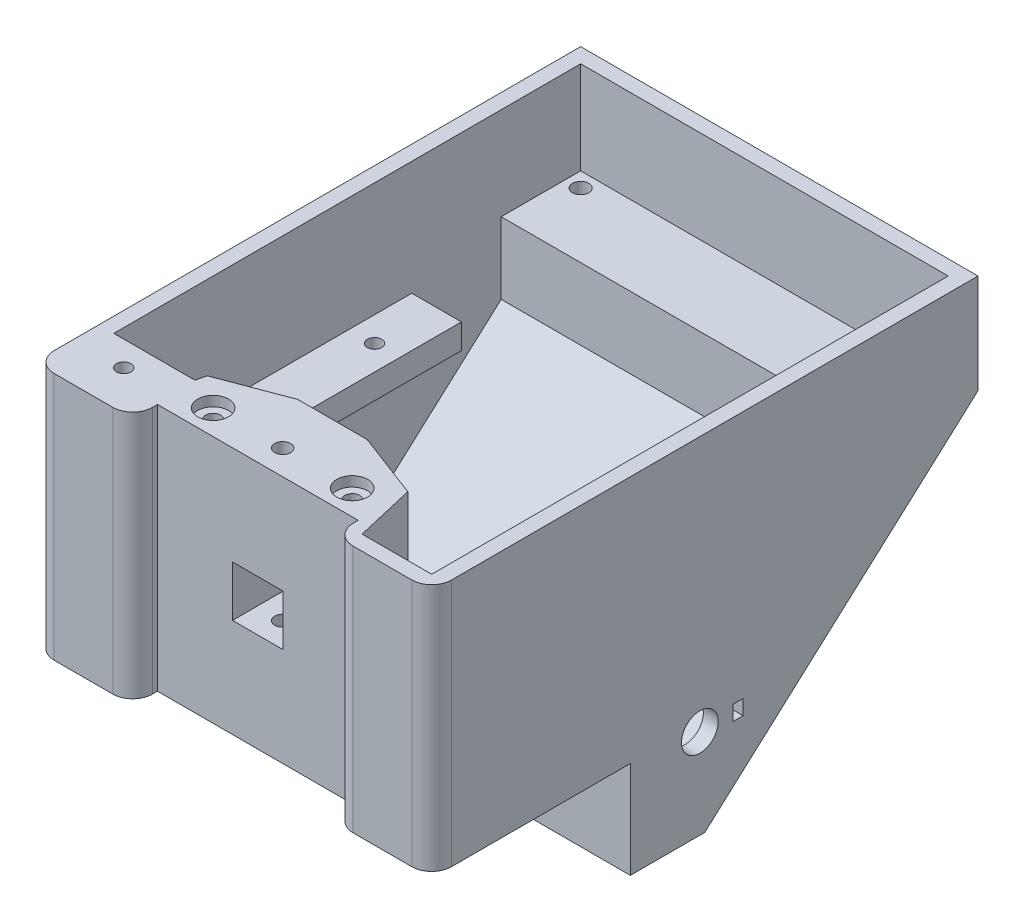
SolidWorks part; units mm, degrees
ref_plane "Спереди" through (0, 0, 0) normal (0, 0, 1) x (1, 0, 0)
ref_plane "Сверху" through (0, 0, 0) normal (0, 1, 0) x (1, 0, 0)
ref_plane "Справа" through (0, 0, 0) normal (1, 0, 0) x (0, 0, -1)
sketch "Sketch2" plane through (0, 0, 0) normal (1, 0, 0) x (0, 0, -1)
  line L0 (-27.3205, 20.9982) -> (-27.3205, -29.0018)
  line L1 (-27.3205, -29.0018) -> (12.6795, -29.0018)
  line L2 (12.6795, -29.0018) -> (12.6795, -48.5114)
  line L3 (12.6795, -48.5114) -> (27.6795, -48.5114)
  line L4 (82.6795, 20.9982) -> (82.6795, 0.9982)
  line L5 (82.6795, 20.9982) -> (-27.3205, 20.9982)
  line L6 (82.6795, 0.9982) -> (27.6795, -48.5114)
  dimension "D1" = 110
  dimension "D2" = 50
  dimension "D3" = 40
  dimension "D4" = 15
  dimension "D5" = 20
extrude "Boss-Extrude1" add sketch "Sketch2" along normal blind 80
shell "Shell1" thickness 3
sketch "Sketch3" plane through (0, 0, 24.3205) normal (0, 0, -1) x (-1, 0, 0)
  line L0 (-40, 20.9982) -> (-40, -26.0018) construction
  line L3 (-77, 20.9982) -> (-3, 20.9982) construction
  line L4 (-77, -26.0018) -> (-3, -26.0018) construction
  line L6 (-17, 20.9982) -> (-63, 20.9982)
  line L7 (-17, 20.9982) -> (-17, -26.0018)
  line L8 (-17, -26.0018) -> (-63, -26.0018)
  line L9 (-63, 20.9982) -> (-63, -26.0018)
  line L10 (-17, 20.9982) -> (-63, -26.0018) construction
  line L11 (-17, -26.0018) -> (-63, 20.9982) construction
  point P6 (-40, -2.5018)
  dimension "D1" = 46
extrude "Boss-Extrude2" add sketch "Sketch3" along normal blind 17
sketch "Sketch4" plane through (0, 0, 27.3205) normal (0, 0, 1) x (1, 0, 0)
  line L0 (0, 20.9982) -> (80, -29.0018) construction
  line L2 (45.1, -9.1018) -> (34.9, -9.1018)
  line L3 (45.1, -9.1018) -> (45.1, 1.0982)
  line L4 (45.1, 1.0982) -> (34.9, 1.0982)
  line L5 (34.9, -9.1018) -> (34.9, 1.0982)
  line L6 (45.1, -9.1018) -> (34.9, 1.0982) construction
  line L7 (45.1, 1.0982) -> (34.9, -9.1018) construction
  point P4 (40, -4.0018)
  dimension "D1" = 10.2
extrude "Cut-Extrude1" cut sketch "Sketch4" against normal up to surface (20 mm away) up to face at (40, -2.5018, 7.3205)
sketch "Sketch6" plane through (0, -29.0018, 0) normal (0, -1, 0) x (1, 0, 0)
  line L0 (40, 27.3205) -> (40, -12.6795) construction
  line L1 (47.5, -5.4795) -> (32.5, -5.4795) construction
  line L2 (47.5, -5.4795) -> (47.5, 7.3205) construction
  line L3 (47.5, 7.3205) -> (32.5, 7.3205) construction
  line L4 (32.5, -5.4795) -> (32.5, 7.3205) construction
  line L5 (47.5, -5.4795) -> (32.5, 7.3205) construction
  line L6 (47.5, 7.3205) -> (32.5, -5.4795) construction
  line L7 (80, -12.6795) -> (0, -12.6795) construction
  line L8 (51.5, 0.9205) -> (28.5, 0.9205) construction
  line L9 (80, 27.3205) -> (0, 27.3205) construction
  line L11 (44, 7.3205) -> (59, 7.3205)
  line L12 (44, 7.3205) -> (44, -5.4795)
  line L13 (44, -5.4795) -> (59, -5.4795)
  line L14 (59, 7.3205) -> (59, -5.4795)
  line L15 (44, 7.3205) -> (59, -5.4795) construction
  line L16 (44, -5.4795) -> (59, 7.3205) construction
  line L17 (36, 7.3205) -> (21, 7.3205)
  line L18 (36, 7.3205) -> (36, -5.4795)
  line L19 (36, -5.4795) -> (21, -5.4795)
  line L20 (21, 7.3205) -> (21, -5.4795)
  line L21 (36, 7.3205) -> (21, -5.4795) construction
  line L22 (36, -5.4795) -> (21, 7.3205) construction
  point P0 (40, 0.9205)
  point P14 (40, 0.9205)
  dimension "D1" = 15
  dimension "D2" = 12.8
  dimension "D3" = 8
  dimension "D4" = 20
extrude "Cut-Extrude2" cut sketch "Sketch6" against normal up to surface (3 mm away) up to face at (40, -26.0018, 10.0705)
sketch "Sketch7" plane through (0, 0, 27.3205) normal (0, 0, 1) x (1, 0, 0)
  line L0 (40, 20.9982) -> (40, -29.0018) construction
  line L1 (80, 20.9982) -> (0, 20.9982) construction
  line L2 (80, -29.0018) -> (0, -29.0018) construction
  line L4 (60.2, -29.0018) -> (19.8, -29.0018)
  line L5 (60.2, -29.0018) -> (60.2, 20.9982)
  line L6 (60.2, 20.9982) -> (19.8, 20.9982)
  line L7 (19.8, -29.0018) -> (19.8, 20.9982)
  line L8 (60.2, -29.0018) -> (19.8, 20.9982) construction
  line L9 (60.2, 20.9982) -> (19.8, -29.0018) construction
  point P6 (40, -4.0018)
  dimension "D1" = 40.4
extrude "Cut-Extrude3" cut sketch "Sketch7" against normal blind 5
fillet "Fillet1" radius 4 4 edges at (19.8, -4.0018, 27.3205) (60.2, -4.0018, 27.3205) (80, -4.0018, 27.3205) (0, -4.0018, 27.3205)
sketch "Sketch12" plane through (0, 20.9982, 0) normal (0, 1, 0) x (1, 0, 0)
  line L0 (19.8, -22.3205) -> (19.8, -12.3205) construction
  line L1 (19.8, -12.3205) -> (60.2, -12.3205) construction
  line L2 (60.2, -12.3205) -> (60.2, -22.3205) construction
  line L3 (33, -7.3205) -> (19.8, -12.3205)
  line L4 (17, -7.3205) -> (63, -7.3205) construction
  line L5 (19.8, -12.3205) -> (17, -24.3205)
  line L6 (17, -24.3205) -> (17, -7.3205)
  line L7 (17, -7.3205) -> (33, -7.3205)
  line L8 (47, -7.3205) -> (63, -7.3205)
  line L9 (63, -7.3205) -> (63, -24.3205)
  line L10 (63, -24.3205) -> (60.2, -12.3205)
  line L11 (60.2, -12.3205) -> (47, -7.3205)
  dimension "D1" = 10
  dimension "D2" = 16
extrude "Cut-Extrude7" cut sketch "Sketch12" against normal up to surface (47 mm away) up to face at (40, -26.0018, 5.4955)
sketch "Sketch13" plane through (0, 20.9982, 0) normal (0, 1, 0) x (1, 0, 0)
  line L0 (19.8, -22.3205) -> (19.8, -12.3205) construction
  line L1 (19.8, -12.3205) -> (60.2, -12.3205) construction
  line L2 (60.2, -12.3205) -> (60.2, -22.3205) construction
  line L3 (60.2, -17.3205) -> (19.8, -17.3205) construction
  circle A0 centre (26, -17.3205) radius 1.5
  circle A1 centre (54, -17.3205) radius 1.5
  point P14 (40, -17.3205)
  dimension "D1" = 3
  dimension "D2" = 28
  dimension "D3" = 14
  dimension "D4" = 6.2
extrude "Cut-Extrude8" cut sketch "Sketch13" against normal blind 25
sketch "Sketch14" plane through (0, 20.9982, 0) normal (0, 1, 0) x (1, 0, 0)
  circle A0 centre (26, -17.3205) radius 3.1
  circle A1 centre (54, -17.3205) radius 3.1
  dimension "D1" = 6.2
extrude "Cut-Extrude9" cut sketch "Sketch14" against normal blind 2
sketch "Sketch17" plane through (77, 0, 0) normal (-1, 0, 0) x (0, 0, 1)
  line L0 (-45.6795, -2.0018) -> (-0.6795, -2.0018)
  line L1 (-0.6795, -2.0018) -> (-0.6795, -7.0018)
  line L2 (-0.6795, -7.0018) -> (-45.6795, -7.0018)
  line L3 (-45.6795, -7.0018) -> (-45.6795, -2.0018)
  line L4 (-79.6795, 20.9982) -> (24.3205, 20.9982) construction
  line L5 (-79.6795, 2.3342) -> (-79.6795, 20.9982) construction
  dimension "D1" = 45
  dimension "D2" = 5
  dimension "D3" = 23
  dimension "D4" = 34
extrude "Boss-Extrude5" add sketch "Sketch17" along normal up to surface (74 mm away) up to face at (3, -14.0994, -24.0865)
sketch "Sketch18" plane through (0, -2.0018, 0) normal (0, 1, 0) x (1, 0, 0)
  line L0 (40, 0.6795) -> (40, 45.6795) construction
  line L1 (3, 0.6795) -> (77, 0.6795) construction
  line L2 (3, 45.6795) -> (77, 45.6795) construction
  line L3 (77, 0.6795) -> (77, 45.6795) construction
  line L4 (13, 0.6795) -> (67, 0.6795)
  line L5 (13, 0.6795) -> (13, 45.6795)
  line L6 (13, 45.6795) -> (67, 45.6795)
  line L7 (67, 0.6795) -> (67, 45.6795)
  line L8 (13, 0.6795) -> (67, 45.6795) construction
  line L9 (13, 45.6795) -> (67, 0.6795) construction
  point P6 (40, 23.1795)
  dimension "D1" = 10
extrude "Cut-Extrude10" cut sketch "Sketch18" against normal up to next
sketch "Sketch19" plane through (0, -2.0018, 0) normal (0, 1, 0) x (1, 0, 0)
  line L0 (72, 45.6795) -> (72, 0.6795) construction
  line L1 (67, 45.6795) -> (77, 45.6795) construction
  line L2 (67, 0.6795) -> (77, 0.6795) construction
  line L3 (8, 45.6795) -> (8, 0.6795) construction
  line L4 (3, 45.6795) -> (13, 45.6795) construction
  line L5 (3, 0.6795) -> (13, 0.6795) construction
  circle A0 centre (72, 37.1795) radius 1.45
  circle A1 centre (72, 6.1795) radius 1.45
  circle A2 centre (8, 33.1795) radius 1.45
  circle A3 centre (8, 6.1795) radius 1.45
  point P20 (72, 23.1795)
  point P21 (8, 23.1795)
  dimension "D1" = 2.9
  dimension "D2" = 14
  dimension "D3" = 17
  dimension "D4" = 17
  dimension "D5" = 10
extrude "Cut-Extrude11" cut sketch "Sketch19" against normal up to next
sketch "Sketch21" plane through (0, -26.0018, 0) normal (0, 1, 0) x (1, 0, 0)
  line L0 (3, -24.3205) -> (3, -14.3205)
  line L1 (3, -24.3205) -> (3, 15.6795) construction
  line L2 (3, -14.3205) -> (19.3333, -14.3205)
  line L3 (19.8, -12.3205) -> (17, -24.3205) construction
  line L4 (19.3333, -14.3205) -> (17, -24.3205)
  line L6 (3, -24.3205) -> (17, -24.3205)
  dimension "D1" = 10
extrude "Boss-Extrude6" add sketch "Sketch21" along normal up to surface (47 mm away) up to face at (54, 20.9982, 20.4205)
sketch "Sketch22" plane through (0, 20.9982, 0) normal (0, 1, 0) x (1, 0, 0)
  line L0 (0, 82.6795) -> (0, -23.3205) construction
  line L1 (15.8, -27.3205) -> (4, -27.3205) construction
  circle A0 centre (10, -19.3205) radius 1.45
  dimension "D1" = 2.9
  dimension "D2" = 10
  dimension "D3" = 8
extrude "Cut-Extrude12" cut sketch "Sketch22" against normal through all
sketch "Sketch24" plane through (80, 0, 0) normal (1, 0, 0) x (0, 0, -1)
  line L0 (12.6795, -48.5114) -> (27.6795, -48.5114) construction
  line L1 (12.6795, -29.0018) -> (12.6795, -48.5114) construction
  line L2 (18.1795, -30.5114) -> (18.1795, -19.0114) construction
  line L3 (18.1795, -19.0114) -> (35.1795, -19.0114) construction
  line L4 (35.1795, -19.0114) -> (35.1795, -30.5114) construction
  line L5 (26.6795, -19.0114) -> (26.6795, -39.0114) construction
  line L6 (30.3795, -30.5114) -> (34.3795, -30.5114) construction
  line L8 (33.3795, -32.0114) -> (35.3795, -32.0114)
  line L9 (33.3795, -32.0114) -> (33.3795, -29.0114)
  line L10 (33.3795, -29.0114) -> (35.3795, -29.0114)
  line L11 (35.3795, -32.0114) -> (35.3795, -29.0114)
  line L12 (33.3795, -32.0114) -> (35.3795, -29.0114) construction
  line L13 (33.3795, -29.0114) -> (35.3795, -32.0114) construction
  circle A0 centre (26.6795, -30.5114) radius 3.7
  circle A1 centre (26.6795, -30.5114) radius 8.5 construction
  dimension "D1" = 7.4
  dimension "D2" = 17
  dimension "D3" = 18
  dimension "D4" = 14
  dimension "D5" = 20
  dimension "D6" = 4
  dimension "D7" = 2
  dimension "D8" = 3
extrude "Cut-Extrude13" cut sketch "Sketch24" against normal up to next
sketch "Sketch26" plane through (3, 0, 0) normal (1, 0, 0) x (0, 0, -1)
  line L0 (79.6795, 2.3342) -> (63.6795, 2.3342)
  line L1 (63.6795, 2.3342) -> (63.6795, -12.0686)
  line L2 (26.5281, -45.5114) -> (79.6795, 2.3342) construction
  line L3 (63.6795, -12.0686) -> (79.6795, 2.3342)
  dimension "D1" = 16
extrude "Boss-Extrude7" add sketch "Sketch26" along normal up to surface (74 mm away) up to face at (77, -30.5114, -34.3795)
sketch "Sketch27" plane through (0, 2.3342, 0) normal (0, 1, 0) x (1, 0, 0)
  line L0 (3, 76.6795) -> (77, 76.6795) construction
  line L1 (3, 79.6795) -> (3, 63.6795) construction
  line L2 (77, 79.6795) -> (77, 63.6795) construction
  line L3 (80, 82.6795) -> (0, 82.6795) construction
  circle A0 centre (6, 76.6795) radius 1.65
  circle A1 centre (74, 76.6795) radius 1.65
  point P10 (40, 76.6795)
  dimension "D1" = 3.3
  dimension "D2" = 68
  dimension "D3" = 34
  dimension "D4" = 6
extrude "Cut-Extrude14" cut sketch "Sketch27" against normal blind 10
sketch "Sketch28" plane through (0, 2.3342, 0) normal (0, 1, 0) x (1, 0, 0)
  line L1 (74, 79.9295) -> (71.1854, 78.3045)
  line L2 (71.1854, 78.3045) -> (71.1854, 75.0545)
  line L3 (71.1854, 75.0545) -> (74, 73.4295)
  line L4 (74, 73.4295) -> (76.8146, 75.0545)
  line L5 (76.8146, 75.0545) -> (76.8146, 78.3045)
  line L6 (76.8146, 78.3045) -> (74, 79.9295)
  line L7 (6, 73.4295) -> (8.8146, 75.0545)
  line L8 (8.8146, 75.0545) -> (8.8146, 78.3045)
  line L9 (8.8146, 78.3045) -> (6, 79.9295)
  line L10 (6, 79.9295) -> (3.1854, 78.3045)
  line L11 (3.1854, 78.3045) -> (3.1854, 75.0545)
  line L12 (3.1854, 75.0545) -> (6, 73.4295)
  circle A0 centre (74, 76.6795) radius 3.25 construction
  circle A1 centre (6, 76.6795) radius 3.25 construction
  dimension "D1" = 6.5
extrude "Cut-Extrude15" cut sketch "Sketch28" against normal blind 32 from offset 3 offset against normal yes
sketch "Sketch29" plane through (0, -29.0018, 0) normal (0, -1, 0) x (1, 0, 0)
  line L0 (0, 23.3205) -> (0, -12.6795) construction
  line L1 (7.1854, 17.6955) -> (10, 16.0705)
  line L2 (10, 16.0705) -> (12.8146, 17.6955)
  line L3 (12.8146, 17.6955) -> (12.8146, 20.9455)
  line L4 (12.8146, 20.9455) -> (10, 22.5705)
  line L5 (10, 22.5705) -> (7.1854, 20.9455)
  line L6 (7.1854, 20.9455) -> (7.1854, 17.6955)
  circle A0 centre (10, 19.3205) radius 3.25 construction
  dimension "D1" = 6.5
extrude "Cut-Extrude16" cut sketch "Sketch29" against normal blind 30
sketch "Sketch30" plane through (0, -26.0018, 0) normal (0, 1, 0) x (1, 0, 0)
  line L0 (77, -24.3205) -> (63, -24.3205)
  line L1 (63, -24.3205) -> (60.2, -12.3205)
  line L2 (63, -24.3205) -> (60.2, -12.3205) construction
  line L3 (60.2, -12.3205) -> (77, -12.3205)
  line L4 (77, -24.3205) -> (77, 15.6795) construction
  line L5 (77, -12.3205) -> (77, -24.3205)
  dimension "D1" = 12
extrude "Boss-Extrude8" add sketch "Sketch30" along normal blind 20
sketch "Sketch31" plane through (0, -6.0018, 0) normal (0, 1, 0) x (1, 0, 0)
  line L0 (76, -27.3205) -> (64.2, -27.3205) construction
  line L1 (80, -23.3205) -> (80, 12.6795) construction
  circle A0 centre (72, -21.3205) radius 1.5
  dimension "D3" = 3
  dimension "D1" = 6
  dimension "D2" = 8
extrude "Cut-Extrude17" cut sketch "Sketch31" against normal through all
sketch "Sketch32" plane through (0, -29.0018, 0) normal (0, -1, 0) x (1, 0, 0)
  line L1 (72, 24.5705) -> (69.1854, 22.9455)
  line L2 (69.1854, 22.9455) -> (69.1854, 19.6955)
  line L3 (69.1854, 19.6955) -> (72, 18.0705)
  line L4 (72, 18.0705) -> (74.8146, 19.6955)
  line L5 (74.8146, 19.6955) -> (74.8146, 22.9455)
  line L6 (74.8146, 22.9455) -> (72, 24.5705)
  circle A0 centre (72, 21.3205) radius 3.25 construction
  dimension "D1" = 6.5
extrude "Cut-Extrude18" cut sketch "Sketch32" against normal blind 15
sketch "Sketch33" plane through (0, -2.0018, 0) normal (0, 1, 0) x (1, 0, 0)
  line L0 (67, 40.6795) -> (77, 40.6795)
  line L1 (67, 0.6795) -> (67, 45.6795) construction
  line L2 (77, 0.6795) -> (77, 45.6795) construction
  line L3 (77, 40.6795) -> (77, 45.6795)
  line L4 (77, 45.6795) -> (67, 45.6795)
  line L5 (67, 45.6795) -> (67, 40.6795)
  dimension "D1" = 5
extrude "Cut-Extrude19" cut sketch "Sketch33" against normal up to next
sketch "Sketch34" plane through (0, 20.9982, 0) normal (0, 1, 0) x (1, 0, 0)
  line L0 (54, -17.3205) -> (26, -17.3205) construction
  circle A0 centre (40, -17.3205) radius 1.6
  dimension "D1" = 3.2
extrude "Cut-Extrude20" cut sketch "Sketch34" against normal through all
sketch "Sketch36" plane through (0, -29.0018, 0) normal (0, -1, 0) x (1, 0, 0)
  line L1 (38.375, 20.1351) -> (36.75, 17.3205)
  line L2 (36.75, 17.3205) -> (38.375, 14.5059)
  line L3 (38.375, 14.5059) -> (41.625, 14.5059)
  line L4 (41.625, 14.5059) -> (43.25, 17.3205)
  line L5 (43.25, 17.3205) -> (41.625, 20.1351)
  line L6 (41.625, 20.1351) -> (38.375, 20.1351)
  circle A0 centre (40, 17.3205) radius 3.25 construction
  dimension "D1" = 6.5
extrude "Cut-Extrude22" cut sketch "Sketch36" against normal blind 14
